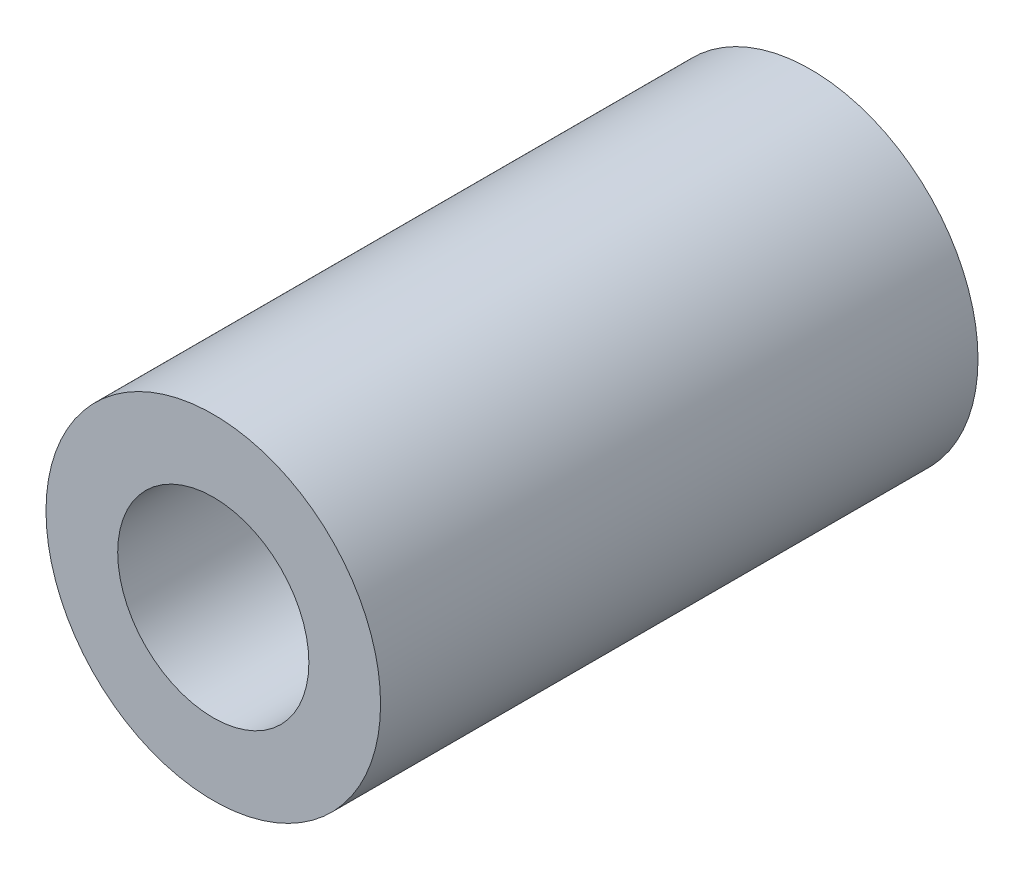
SolidWorks part; units mm, degrees
material "1060 Alloy"
ref_plane "Front Plane" through (0, 0, 0) normal (1, 0, 0) x (0, 1, 0)
ref_plane "Top Plane" through (0, 0, 0) normal (0, 0, 1) x (0, 1, 0)
ref_plane "Right Plane" through (0, 0, 0) normal (0, 1, 0) x (-1, 0, 0)
sketch "Sketch1" plane through (0, 0, 0) normal (0, 0, 1) x (0, 1, 0)
  circle A0 centre (0, 0) radius 7
  circle A1 centre (0, 0) radius 3
  dimension "D1" = 6
  dimension "D2" = 14
extrude "Boss-Extrude1" add sketch "Sketch1" along normal blind 25
sketch "Sketch2" plane through (0, 0, 25) normal (0, 0, 1) x (1, 0, 0)
sketch "Sketch3" plane through (0, 0, 25) normal (0, 0, 1) x (1, 0, 0)
  circle A0 centre (0, 0) radius 4
extrude "Cut-Extrude1" cut sketch "Sketch3" against normal blind 13
